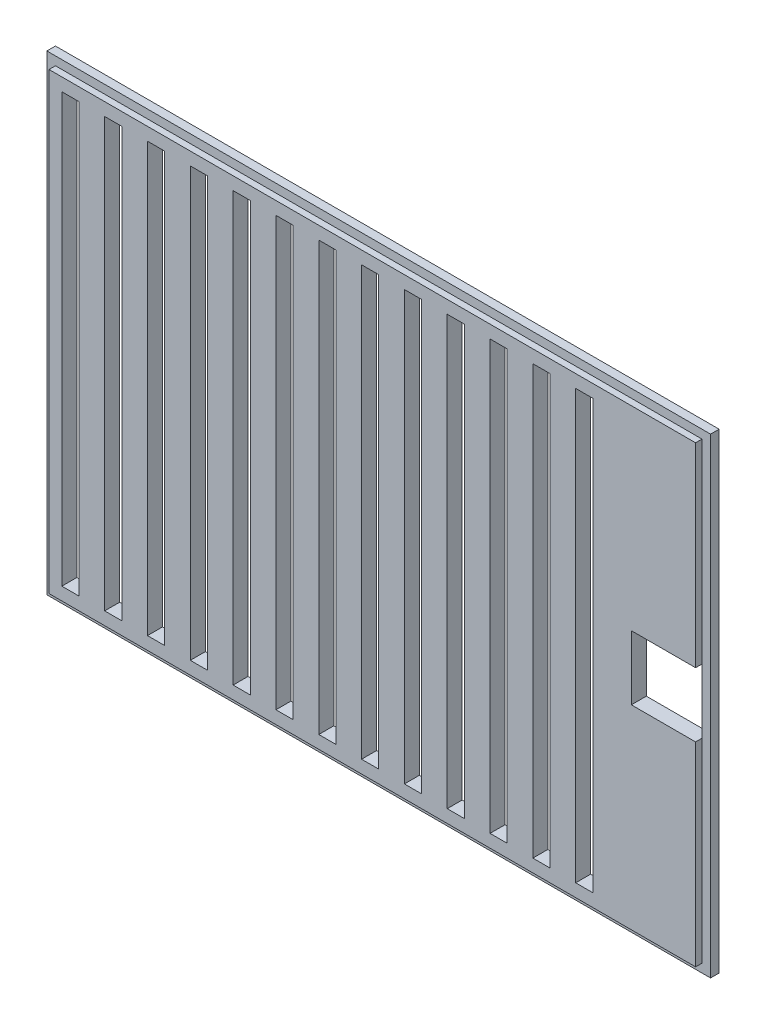
SolidWorks part; units mm, degrees
ref_plane "Front Plane" through (0, 0, 0) normal (0, 0, 1) x (1, 0, 0)
ref_plane "Top Plane" through (0, 0, 0) normal (0, 1, 0) x (1, 0, 0)
ref_plane "Right Plane" through (0, 0, 0) normal (1, 0, 0) x (0, 0, -1)
sketch "Sketch1" plane through (0, 0, 0) normal (0, 0, 1) x (1, 0, 0)
  line L1 (0, 0) -> (155, 0)
  line L2 (0, 0) -> (0, 110)
  line L3 (0, 110) -> (155, 110)
  line L4 (155, 0) -> (155, 110)
  dimension "D1" = 110
  dimension "D2" = 155
extrude "Boss-Extrude1" add sketch "Sketch1" along normal blind 2
sketch "Sketch2" plane through (0, 0, 2) normal (0, 0, 1) x (1, 0, 0)
  line L0 (0, 110) -> (2, 110) construction
  line L1 (155, 110) -> (0, 110) construction
  line L2 (2, 110) -> (2, 108) construction
  line L3 (155, 0) -> (153, 0) construction
  line L4 (0, 0) -> (155, 0) construction
  line L5 (153, 0) -> (153, 2) construction
  line L7 (2, 108) -> (153, 108)
  line L8 (2, 108) -> (2, 2)
  line L9 (2, 2) -> (153, 2)
  line L10 (153, 108) -> (153, 2)
  dimension "D1" = 2
  dimension "D2" = 2
  dimension "D3" = 2
  dimension "D4" = 2
extrude "Boss-Extrude2" add sketch "Sketch2" along normal blind 1.5
sketch "Sketch3" plane through (0, 0, 3.5) normal (0, 0, 1) x (1, 0, 0)
  line L0 (153, 55) -> (2, 55) construction
  line L1 (153, 2) -> (153, 108) construction
  line L2 (2, 108) -> (2, 2) construction
  line L3 (153, 55) -> (153, 62.5) construction
  line L4 (153, 62.5) -> (138, 62.5) construction
  line L6 (138, 62.5) -> (153, 62.5)
  line L7 (138, 62.5) -> (138, 47.5)
  line L8 (138, 47.5) -> (153, 47.5)
  line L9 (153, 62.5) -> (153, 47.5)
  dimension "D1" = 7.5
  dimension "D2" = 15
  dimension "D3" = 15
extrude "Cut-Extrude2" cut sketch "Sketch3" against normal blind 3.5
sketch "Sketch5" plane through (0, 0, 3.5) normal (0, 0, 1) x (1, 0, 0)
  line L0 (2, 55) -> (153, 55) construction
  line L1 (2, 108) -> (2, 2) construction
  line L2 (153, 62.5) -> (153, 47.5) construction
  line L3 (153, 108) -> (133, 108) construction
  line L4 (153, 108) -> (2, 108) construction
  line L5 (2, 108) -> (5, 108) construction
  line L6 (5, 108) -> (9, 108) construction
  line L7 (5, 108) -> (5, 105) construction
  line L8 (5, 2) -> (5, 5) construction
  line L9 (2, 2) -> (153, 2) construction
  line L10 (15, 5) -> (15, 105)
  line L11 (5, 5) -> (9, 5)
  line L12 (5, 5) -> (5, 105)
  line L13 (5, 105) -> (9, 105)
  line L14 (9, 5) -> (9, 105)
  line L15 (15, 5) -> (19, 5)
  line L16 (19, 5) -> (19, 105)
  line L17 (15, 105) -> (19, 105)
  line L18 (25, 5) -> (25, 105)
  line L19 (25, 5) -> (29, 5)
  line L20 (29, 5) -> (29, 105)
  line L21 (25, 105) -> (29, 105)
  line L22 (35, 5) -> (35, 105)
  line L23 (35, 5) -> (39, 5)
  line L24 (39, 5) -> (39, 105)
  line L25 (35, 105) -> (39, 105)
  line L26 (45, 5) -> (45, 105)
  line L27 (45, 5) -> (49, 5)
  line L28 (49, 5) -> (49, 105)
  line L29 (45, 105) -> (49, 105)
  line L30 (55, 5) -> (55, 105)
  line L31 (55, 5) -> (59, 5)
  line L32 (59, 5) -> (59, 105)
  line L33 (55, 105) -> (59, 105)
  line L34 (65, 5) -> (65, 105)
  line L35 (65, 5) -> (69, 5)
  line L36 (69, 5) -> (69, 105)
  line L37 (65, 105) -> (69, 105)
  line L38 (75, 5) -> (75, 105)
  line L39 (75, 5) -> (79, 5)
  line L40 (79, 5) -> (79, 105)
  line L41 (75, 105) -> (79, 105)
  line L42 (85, 5) -> (85, 105)
  line L43 (85, 5) -> (89, 5)
  line L44 (89, 5) -> (89, 105)
  line L45 (85, 105) -> (89, 105)
  line L46 (95, 5) -> (95, 105)
  line L47 (95, 5) -> (99, 5)
  line L48 (99, 5) -> (99, 105)
  line L49 (95, 105) -> (99, 105)
  line L50 (105, 5) -> (105, 105)
  line L51 (105, 5) -> (109, 5)
  line L52 (109, 5) -> (109, 105)
  line L53 (105, 105) -> (109, 105)
  line L54 (115, 5) -> (115, 105)
  line L55 (115, 5) -> (119, 5)
  line L56 (119, 5) -> (119, 105)
  line L57 (115, 105) -> (119, 105)
  line L58 (125, 5) -> (125, 105)
  line L59 (125, 5) -> (129, 5)
  line L60 (129, 5) -> (129, 105)
  line L61 (125, 105) -> (129, 105)
  dimension "D1" = 20
  dimension "D2" = 3
  dimension "D3" = 4
  dimension "D4" = 3
  dimension "D5" = 3
extrude "Cut-Extrude3" cut sketch "Sketch5" against normal blind 3.5
